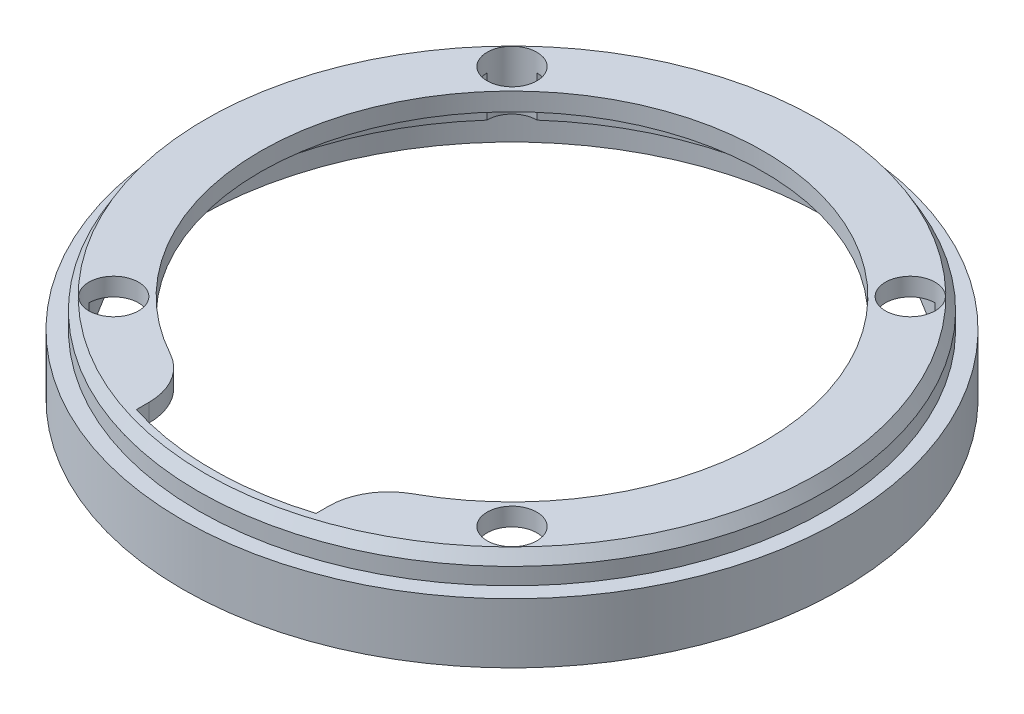
SolidWorks part; units mm, degrees
ref_plane "Спереди" through (0, 0, 0) normal (0, 0, 1) x (1, 0, 0)
ref_plane "Сверху" through (0, 0, 0) normal (0, 1, 0) x (1, 0, 0)
ref_plane "Справа" through (0, 0, 0) normal (1, 0, 0) x (0, 0, -1)
sketch "Sketch1" plane through (0, 0, 0) normal (0, 1, 0) x (1, 0, 0)
  circle A0 centre (0, 0) radius 55
  dimension "D1" = 110
extrude "Boss-Extrude1" add sketch "Sketch1" along normal blind 14.8
shell "Shell1" thickness 5
sketch "Sketch2" plane through (0, 9.8, 0) normal (0, -1, 0) x (1, 0, 0)
  circle A0 centre (0, 0) radius 35
  dimension "D1" = 70
extrude "Cut-Extrude1" cut sketch "Sketch2" against normal through all
sketch "Sketch3" plane through (0, 14.8, 0) normal (0, 1, 0) x (1, 0, 0)
  circle A0 centre (0, 0) radius 42
  dimension "D1" = 84
extrude "Cut-Extrude2" cut sketch "Sketch3" against normal through all
sketch "Sketch4" plane through (0, 14.8, 0) normal (0, 1, 0) x (1, 0, 0)
  line L1 (-33.234, 33.234) -> (33.234, 33.234) construction
  line L2 (-33.234, 33.234) -> (-33.234, -33.234) construction
  line L3 (-33.234, -33.234) -> (33.234, -33.234) construction
  line L4 (33.234, 33.234) -> (33.234, -33.234) construction
  line L5 (-33.234, 33.234) -> (33.234, -33.234) construction
  line L6 (-33.234, -33.234) -> (33.234, 33.234) construction
  circle A0 centre (0, 0) radius 55 construction
  circle A2 centre (-33.234, -33.234) radius 4.15
  circle A3 centre (-33.234, 33.234) radius 4.15
  circle A4 centre (33.234, 33.234) radius 4.15
  circle A5 centre (33.234, -33.234) radius 4.15
  circle A6 centre (0, 0) radius 47 construction
  dimension "D2" = 8.3
  dimension "D3" = 8
extrude "Cut-Extrude3" cut sketch "Sketch4" against normal through all
sketch "Sketch6" plane through (0, 9.8, 0) normal (0, -1, 0) x (1, 0, 0)
  circle A0 centre (0, 0) radius 50
extrude "Cut-Extrude4" cut sketch "Sketch6" against normal blind 2
sketch "Sketch7" plane through (0, 11.8, 0) normal (0, -1, 0) x (1, 0, 0)
  line L0 (33.234, 33.234) -> (-33.234, 33.234) construction
  line L1 (0, 33.234) -> (0, 50) construction
  line L2 (15, 33.234) -> (15, 47.697)
  line L3 (-15, 33.234) -> (-15, 47.697)
  line L4 (15, 33.234) -> (-15, 33.234)
  arc A0 (33.2031, 37.3839) -> (-33.2031, 37.3839) centre (0, 0) ccw construction
  arc A1 (15, 47.697) -> (-15, 47.697) centre (0, 0) ccw
  point P14 (0, 33.234)
  dimension "D1" = 30
extrude "Cut-Extrude5" cut sketch "Sketch7" against normal through all
fillet "Fillet1" radius 10 2 edges at (-15, 13.3, 39.2301) (15, 13.3, 39.2301)
sketch "Sketch8" plane through (0, 14.8, 0) normal (0, 1, 0) x (1, 0, 0)
  circle A0 centre (0, 0) radius 52.35
  dimension "D1" = 104.7
extrude "Cut-Extrude6" cut sketch "Sketch8" against normal blind 4.8 flip side to cut
chamfer "Chamfer1" distance 2 angle 30 1 edges at (0, 14.8, 52.35)
sketch "Sketch9" plane through (0, 0, 0) normal (0, -1, 0) x (1, 0, 0)
  circle A0 centre (0, 0) radius 52.5
  dimension "D1" = 105
extrude "Cut-Extrude7" cut sketch "Sketch9" against normal blind 5
